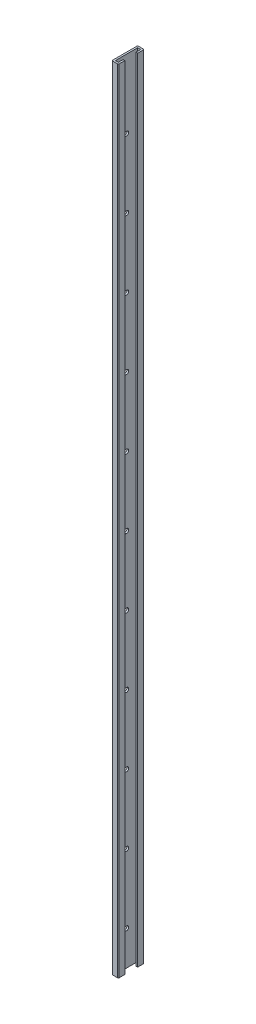
SolidWorks part; units mm, degrees
ref_plane "Front" through (0, 0, 0) normal (0, 0, 1) x (1, 0, 0)
ref_plane "Top" through (0, 0, 0) normal (0, 1, 0) x (1, 0, 0)
ref_plane "Right" through (0, 0, 0) normal (1, 0, 0) x (0, 0, -1)
sketch "Sketch1" plane through (0, 0, 0) normal (0, 1, 0) x (1, 0, 0)
  line L0 (9.525, 34.29) -> (9.525, 26.035)
  line L1 (1.27, -2.54) -> (8.255, -2.54)
  line L2 (0, -1.27) -> (0, 34.29)
  line L3 (1.27, 35.56) -> (8.255, 35.56)
  line L5 (9.525, -1.27) -> (9.525, 6.985)
  line L6 (6.985, 0) -> (6.985, 6.985)
  line L7 (2.54, 0) -> (6.985, 0)
  line L8 (2.54, 0) -> (2.54, 33.02)
  line L9 (2.54, 33.02) -> (6.985, 33.02)
  line L10 (6.985, 33.02) -> (6.985, 26.035)
  line L11 (9.525, 6.985) -> (6.985, 6.985)
  line L12 (9.525, 26.035) -> (6.985, 26.035)
  line L13 (0, -2.54) -> (0, 35.56) construction
  line L14 (0, 35.56) -> (9.525, 35.56) construction
  line L15 (0, -2.54) -> (9.525, -2.54) construction
  line L16 (9.525, -2.54) -> (9.525, 6.985) construction
  line L17 (9.525, 35.56) -> (9.525, 26.035) construction
  arc A0 (0, 34.29) -> (1.27, 35.56) centre (1.27, 34.29) cw
  arc A1 (1.27, -2.54) -> (0, -1.27) centre (1.27, -1.27) cw
  arc A2 (8.255, -2.54) -> (9.525, -1.27) centre (8.255, -1.27) ccw
  arc A3 (8.255, 35.56) -> (9.525, 34.29) centre (8.255, 34.29) cw
  point P16 (0, 35.56)
  dimension "D5" = 1.27
  dimension "D1" = 38.1
  dimension "D2" = 9.525
  dimension "D3" = 9.525
  dimension "D4" = 2.54
extrude "Boss-Extrude1" add sketch "Sketch1" along normal blind 1168.4
sketch "Sketch2" plane through (2.54, 0, 0) normal (1, 0, 0) x (0, 0, -1)
  line L0 (16.51, 50.8) -> (16.51, 0) construction
  line L1 (34.29, 0) -> (-1.27, 0) construction
  circle A0 centre (16.51, 50.8) radius 3.175
  circle A1 centre (16.51, 152.4) radius 3.175
  circle A2 centre (16.51, 254) radius 3.175
  circle A3 centre (16.51, 355.6) radius 3.175
  circle A4 centre (16.51, 457.2) radius 3.175
  circle A5 centre (16.51, 558.8) radius 3.175
  circle A6 centre (16.51, 660.4) radius 3.175
  circle A7 centre (16.51, 762) radius 3.175
  circle A8 centre (16.51, 863.6) radius 3.175
  circle A9 centre (16.51, 965.2) radius 3.175
  circle A10 centre (16.51, 1066.8) radius 3.175
  dimension "D1" = 6.35
  dimension "D2" = 50.8
  dimension "D3" = 11
extrude "Cut-Extrude1" cut sketch "Sketch2" against normal up to next
